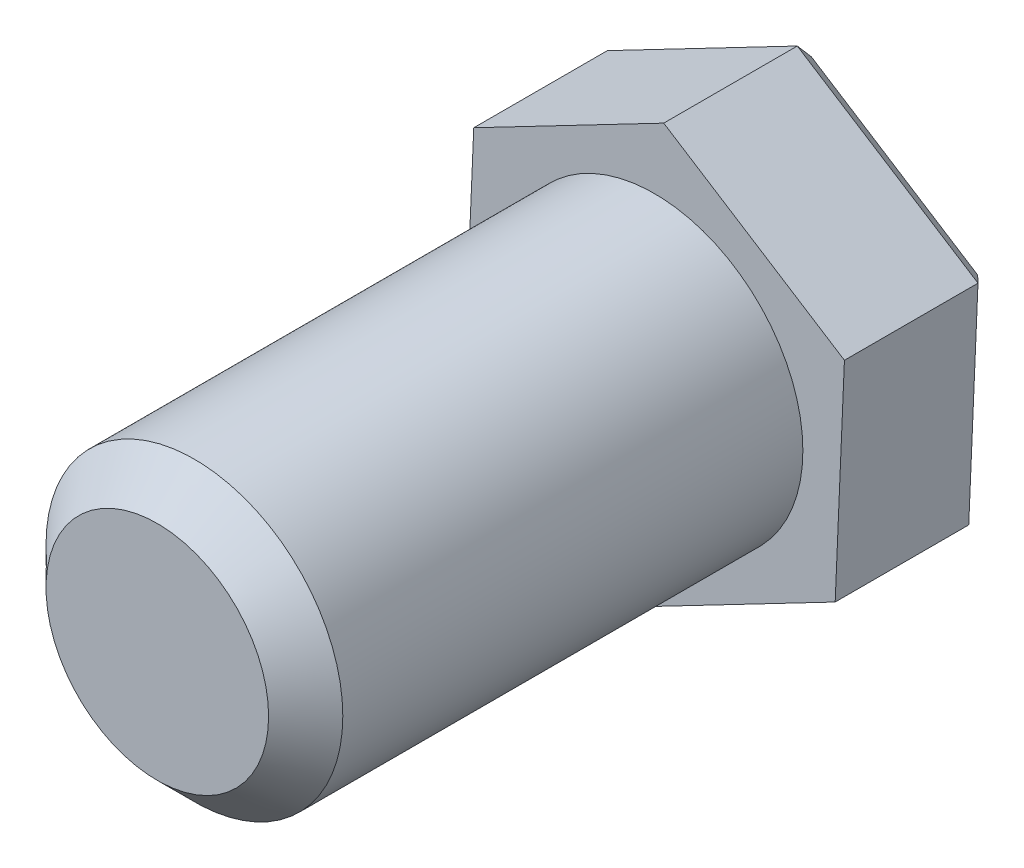
SolidWorks part; units mm, degrees
ref_plane "Front Plane" through (0, 0, 0) normal (0, 0, 1) x (1, 0, 0)
ref_plane "Top Plane" through (0, 0, 0) normal (0, 1, 0) x (1, 0, 0)
ref_plane "Right Plane" through (0, 0, 0) normal (1, 0, 0) x (0, 0, -1)
sketch "Sketch1" plane through (0, 0, 0) normal (0, 0, 1) x (1, 0, 0)
  circle A0 centre (0, 0) radius 2
extrude "Boss-Extrude1" add sketch "Sketch1" along normal blind 6.7
sketch "Sketch2" plane through (0, 0, 0) normal (0, 0, -1) x (-1, 0, 0)
  line L7 (0.1248, -2.8841) -> (2.5601, -1.3339)
  line L8 (2.5601, -1.3339) -> (2.4353, 1.5501)
  line L9 (2.4353, 1.5501) -> (-0.1248, 2.8841)
  line L10 (-0.1248, 2.8841) -> (-2.5601, 1.3339)
  line L11 (-2.5601, 1.3339) -> (-2.4353, -1.5501)
  line L12 (-2.4353, -1.5501) -> (0.1248, -2.8841)
  circle A0 centre (0, 0) radius 2.5 construction
  dimension "D1" = 5
  dimension "D2" = 5.7681
chamfer "Chamfer1" distance 0.5 angle 45 1 edges at (2, 0, 6.7)
extrude "Boss-Extrude2" add sketch "Sketch2" along normal blind 2
chamfer "Chamfer2" distance 0.2 angle 45 6 edges at (2.4977, -0.1081, -2) (1.3424, 2.109, -2) (-1.1552, 2.2171, -2) (-2.4977, 0.1081, -2) (-1.3424, -2.109, -2) (1.1552, -2.2171, -2)
